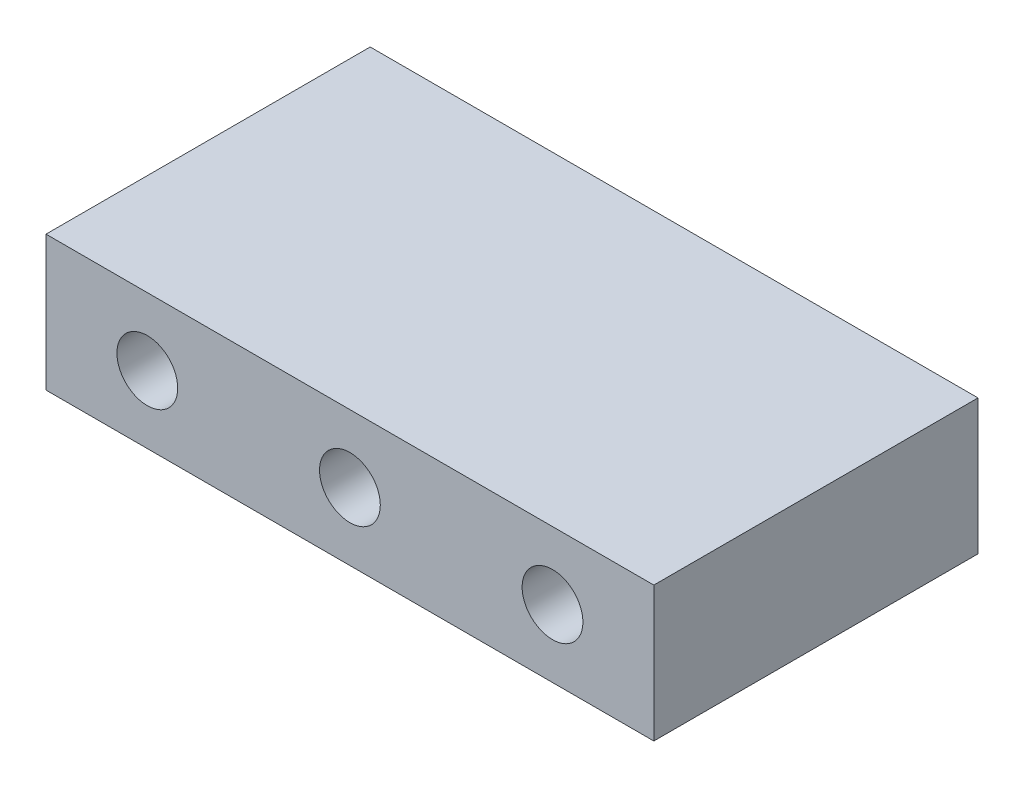
SolidWorks part; units mm, degrees
material "ABS"
ref_plane "前视基准面" through (0, 0, 0) normal (0, 0, 1) x (1, 0, 0)
ref_plane "上视基准面" through (0, 0, 0) normal (0, 1, 0) x (1, 0, 0)
ref_plane "右视基准面" through (0, 0, 0) normal (1, 0, 0) x (0, 0, -1)
sketch "草图1" plane through (0, 0, 0) normal (0, 0, 1) x (1, 0, 0)
  line L0 (-45, 0) -> (-30, 0) construction
  line L1 (-45, 10) -> (45, 10)
  line L2 (-45, 10) -> (-45, -10)
  line L3 (-45, -10) -> (45, -10)
  line L4 (45, 10) -> (45, -10)
  line L5 (-45, 10) -> (45, -10) construction
  line L6 (-45, -10) -> (45, 10) construction
  line L7 (45, 0) -> (30, 0) construction
  circle A0 centre (-30, 0) radius 4.5
  circle A1 centre (0, 0) radius 4.5
  circle A2 centre (30, 0) radius 4.5
  point P0 (0, 0)
extrude "凸台-拉伸1" add sketch "草图1" along normal blind 48
